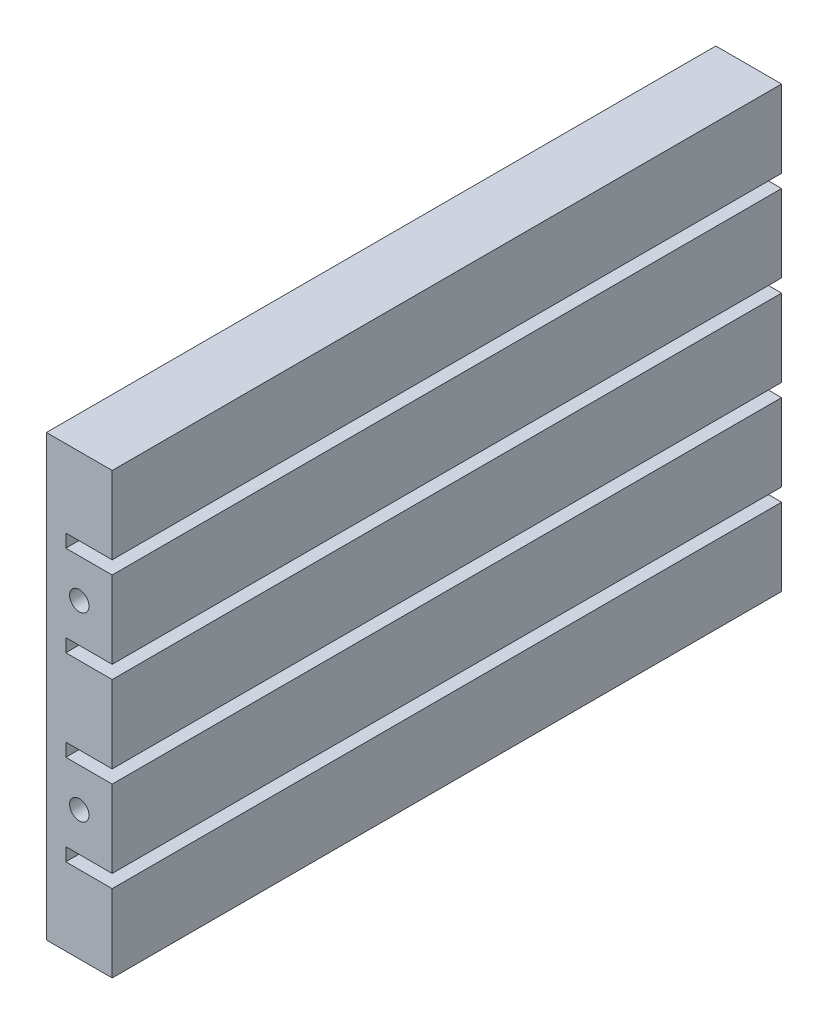
SolidWorks part; units mm, degrees
material "6061-T6 (SS)"
ref_plane "Front Plane" through (0, 0, 0) normal (0, 0, 1) x (1, 0, 0)
ref_plane "Top Plane" through (0, 0, 0) normal (0, 1, 0) x (1, 0, 0)
ref_plane "Right Plane" through (0, 0, 0) normal (1, 0, 0) x (0, 0, -1)
sketch "Sketch1" plane through (0, 0, 0) normal (0, 0, 1) x (1, 0, 0)
  line L0 (0, 0) -> (0, 56.8)
  line L1 (0, 56.8) -> (8.5, 56.8)
  line L2 (8.5, 56.8) -> (8.5, 46.8)
  line L3 (8.5, 46.8) -> (2.5, 46.8)
  line L4 (2.5, 46.8) -> (2.5, 45.1)
  line L5 (2.5, 45.1) -> (8.5, 45.1)
  line L6 (8.5, 45.1) -> (8.5, 35.1)
  line L7 (8.5, 35.1) -> (2.5, 35.1)
  line L8 (2.5, 35.1) -> (2.5, 33.4)
  line L9 (2.5, 33.4) -> (8.5, 33.4)
  line L10 (8.5, 33.4) -> (8.5, 23.4)
  line L11 (8.5, 23.4) -> (2.5, 23.4)
  line L12 (2.5, 23.4) -> (2.5, 21.7)
  line L13 (2.5, 21.7) -> (8.5, 21.7)
  line L14 (8.5, 21.7) -> (8.5, 11.7)
  line L15 (8.5, 11.7) -> (2.5, 11.7)
  line L16 (2.5, 11.7) -> (2.5, 10)
  line L17 (2.5, 10) -> (8.5, 10)
  line L18 (8.5, 10) -> (8.5, 0)
  line L19 (8.5, 0) -> (0, 0)
  dimension "D1" = 56.8
  dimension "D2" = 8.5
  dimension "D3" = 10
  dimension "D4" = 1.7
  dimension "D5" = 6
  dimension "D6" = 10
  dimension "D7" = 1.7
  dimension "D8" = 10
  dimension "D9" = 10
  dimension "D10" = 1.7
  dimension "D11" = 1.7
  dimension "D12" = 2.5
  dimension "D13" = 2.5
  dimension "D14" = 2.5
  dimension "D15" = 8.5
  dimension "D16" = 8.5
  dimension "D17" = 8.5
  dimension "D18" = 8.5
extrude "Boss-Extrude1" add sketch "Sketch1" along normal blind 86.5
sketch "Sketch2" plane through (0, 0, 86.5) normal (0, 0, 1) x (1, 0, 0)
  line L0 (8.5, 35.1) -> (8.5, 45.1) construction
  line L6 (2.5, 35.1) -> (8.5, 35.1) construction
  line L8 (8.5, 11.7) -> (8.5, 21.7) construction
  line L9 (8.5, 21.7) -> (2.5, 21.7) construction
  point P0 (4.25, 16.7)
  point P11 (4.25, 40.1)
  dimension "D1" = 4.25
  dimension "D2" = 5
  dimension "D3" = 4.25
  dimension "D4" = 5
hole_wizard "M3x0.5 Tapped Hole2" positions "Sketch3" profile "Sketch4" tap size "M3x0.5" standard "ANSI Metric"
sketch "Sketch3" plane through (0, 0, 86.5) normal (0, 0, 1) x (1, 0, 0)
  point P0 (4.25, 40.1)
  point P3 (4.25, 16.7)
sketch "Sketch4" plane through (4.25, 40.1, 86.5) normal (1, 0, 0) x (0, -1, 0)
  line L0 (0, 0) -> (0, 5.7511)
  line L1 (0, 5.7511) -> (1.25, 5)
  line L2 (1.25, 5) -> (1.25, 0)
  line L5 (1.25, 0) -> (0, 0)
  line L10 (0, 5.7511) -> (-1.25, 5) construction
  line L11 (0, -6.35) -> (0, 107.95) construction
  dimension "Tap Drill Dia." = 2.5
  dimension "Tap Drill Depth" = 5
  dimension "Drill Angle" = 118
ref_plane "Plane1" through (0, 0, 43.25) normal (0, 0, 1) x (1, 0, 0)
mirror "Mirror1" about plane through (0, 0, 43.25) normal (0, 0, 1) of "M3x0.5 Tapped Hole2"
sketch "Sketch5" plane through (0, 0, 0) normal (-1, 0, 0) x (0, 0, 1)
  line L1 (86.5, 56.8) -> (0, 56.8) construction
  line L5 (0, 56.8) -> (0, 0) construction
  line L7 (86.5, 0) -> (0, 0) construction
  line L8 (86.5, 56.8) -> (86.5, 0) construction
  point P0 (78.25, 5)
  point P3 (8.25, 5)
  point P4 (8.25, 51.8)
  point P7 (78.25, 51.8)
  dimension "D1" = 5
  dimension "D2" = 8.25
  dimension "D3" = 70
  dimension "D4" = 5
  dimension "D5" = 5
  dimension "D6" = 8.25
  dimension "D7" = 8.25
  dimension "D8" = 5
hole_wizard "M3x0.5 Tapped Hole1" positions "Sketch10" profile "Sketch11" tap size "M3x0.5" standard "ANSI Metric"
sketch "Sketch10" plane through (0, 0, 0) normal (-1, 0, 0) x (0, 0, 1)
  line L0 (43.25, 56.8) -> (43.25, 0) construction
  line L1 (86.5, 56.8) -> (0, 56.8) construction
  line L2 (86.5, 0) -> (0, 0) construction
  line L7 (43.25, 51.8) -> (8.25, 51.8) construction
  line L12 (43.25, 5) -> (8.25, 5) construction
  point P16 (8.25, 51.8)
  point P26 (8.25, 5)
sketch "Sketch11" plane through (0, 5, 8.25) normal (0, 1, 0) x (0, 0, 1)
  line L0 (0, 0) -> (0, 4.7511)
  line L1 (0, 4.7511) -> (1.25, 4)
  line L2 (1.25, 4) -> (1.25, 0)
  line L5 (1.25, 0) -> (0, 0)
  line L10 (0, 4.7511) -> (-1.25, 4) construction
  line L11 (0, -6.35) -> (0, 107.95) construction
  dimension "Tap Drill Dia." = 2.5
  dimension "Tap Drill Depth" = 4
  dimension "Drill Angle" = 118
ref_plane "Plane2" through (0, 0, 43.25) normal (0, 0, -1) x (-1, 0, 0)
mirror "Mirror2" about plane through (0, 0, 43.25) normal (0, 0, -1) of "M3x0.5 Tapped Hole1"
